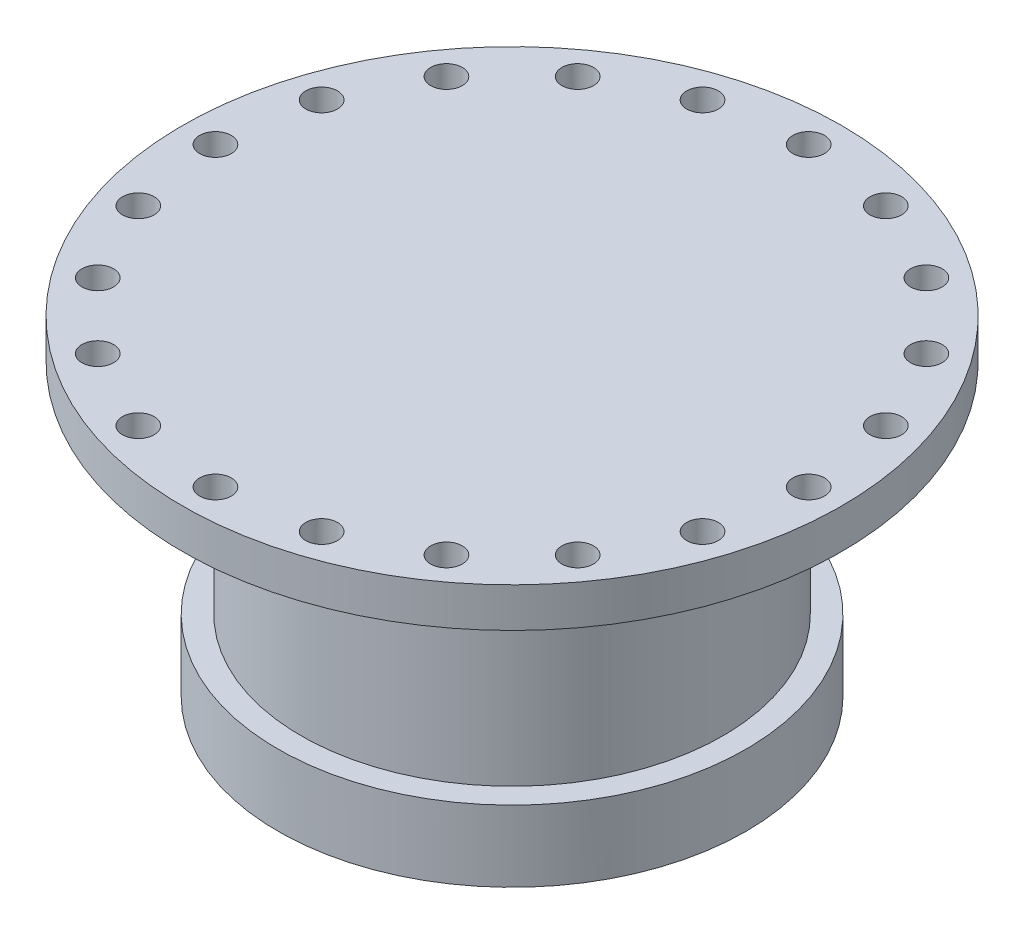
SolidWorks part; units mm, degrees
ref_plane "Plano frontal" through (0, 0, 0) normal (0, 0, 1) x (1, 0, 0)
ref_plane "Plano superior" through (0, 0, 0) normal (0, 1, 0) x (1, 0, 0)
ref_plane "Plano direito" through (0, 0, 0) normal (1, 0, 0) x (0, 0, -1)
sketch "Esboço1" plane through (0, 0, 0) normal (0, 0, 1) x (1, 0, 0)
  line L1 (177.5, 3946.0099) -> (406.352, 3946.0099) construction
  line L2 (0, 4196) -> (250, 4196)
  line L3 (250, 4196) -> (250, 4166)
  line L4 (250, 4166) -> (180, 4166)
  line L5 (160, 4160) -> (160, 4000)
  line L6 (160, 4000) -> (177.5, 4000)
  line L7 (177.5, 4000) -> (177.5, 3946.0099)
  line L9 (0, 4196) -> (0, 4160)
  line L10 (180, 4166) -> (174, 4160)
  line L11 (174, 4160) -> (160, 4160)
  line L12 (0, 4160) -> (140, 4160)
  line L13 (140, 4160) -> (140, 4000)
  line L14 (140, 4000) -> (0, 4000)
  line L15 (0, 113.6567) -> (0, 165.1472) construction
  line L16 (0, 4000) -> (0, 3950)
  arc A0 (177.5, 3946.0099) -> (0, 3950) centre (0, 0) ccw
  dimension "D3" = 7900
  dimension "D1" = 250
  dimension "D2" = 30
  dimension "D4" = 4196
  dimension "D5" = 70
  dimension "D6" = 6
  dimension "D7" = 6
  dimension "D8" = 160
  dimension "D9" = 140
  dimension "D10" = 160
  dimension "D11" = 177.5
revolve "Revolução1" add sketch "Esboço1" angle 360 about L15
sketch "Esboço2" plane through (0, 4196, 0) normal (0, 1, 0) x (1, 0, 0)
  circle A0 centre (0, 225) radius 12
  circle A1 centre (69.5288, 213.9877) radius 12
  circle A2 centre (132.2517, 182.0288) radius 12
  circle A3 centre (182.0288, 132.2517) radius 12
  circle A4 centre (213.9877, 69.5288) radius 12
  circle A5 centre (225, 0) radius 12
  circle A6 centre (213.9877, -69.5288) radius 12
  circle A7 centre (182.0288, -132.2517) radius 12
  circle A8 centre (132.2517, -182.0288) radius 12
  circle A9 centre (69.5288, -213.9877) radius 12
  circle A10 centre (0, -225) radius 12
  circle A11 centre (-69.5288, -213.9877) radius 12
  circle A12 centre (-132.2517, -182.0288) radius 12
  circle A13 centre (-182.0288, -132.2517) radius 12
  circle A14 centre (-213.9877, -69.5288) radius 12
  circle A15 centre (-225, 0) radius 12
  circle A16 centre (-213.9877, 69.5288) radius 12
  circle A17 centre (-182.0288, 132.2517) radius 12
  circle A18 centre (-132.2517, 182.0288) radius 12
  circle A19 centre (-69.5288, 213.9877) radius 12
  point P44 (0, 0)
  dimension "D1" = 24
  dimension "D2" = 225
  dimension "D3" = 20
extrude "Corte-extrusão1" cut sketch "Esboço2" against normal through all
